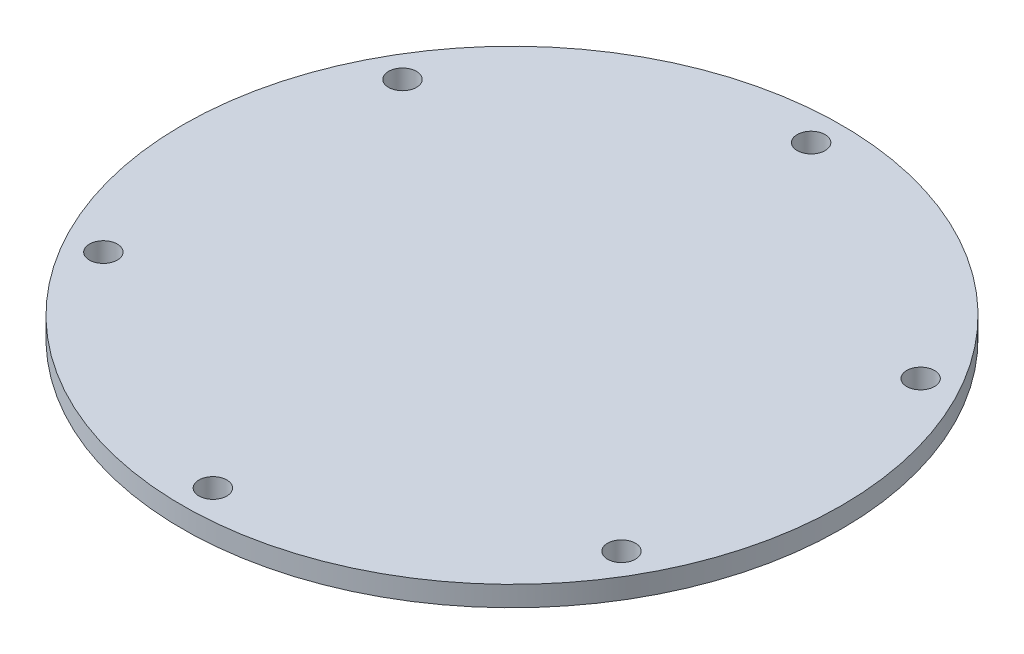
SolidWorks part; units mm, degrees
ref_plane "Alzado" through (0, 0, 0) normal (0, 0, 1) x (1, 0, 0)
ref_plane "Planta" through (0, 0, 0) normal (0, 1, 0) x (1, 0, 0)
ref_plane "Vista lateral" through (0, 0, 0) normal (1, 0, 0) x (0, 0, -1)
sketch "Croquis1" plane through (0, 0, 0) normal (0, 0, 1) x (1, 0, 0)
  line L0 (0, 59.498) -> (0, -59.498) construction
  line L1 (0, 0) -> (-65, 0)
  line L2 (-65, 0) -> (-65, -4)
  line L3 (-65, -4) -> (-44, -4)
  line L4 (-44, -4) -> (-44, -6)
  line L5 (-44, -6) -> (-41, -6)
  line L6 (-41, -6) -> (-41, -4)
  line L7 (-41, -4) -> (0, -4)
  line L8 (0, 0) -> (0, -4)
  point P6 (0, 0)
  dimension "D1" = 65
  dimension "D2" = 4
  dimension "D3" = 6
  dimension "D4" = 44
  dimension "D5" = 3
revolve "Revolución1" add sketch "Croquis1" angle 360 about L0
hole_wizard "Taladro de margen para M51" positions "Croquis4" profile "Croquis5" hole size "M5" standard "DIN"
sketch "Croquis4" plane through (0, -4, 0) normal (0, -1, 0) x (-1, 0, 0)
  circle A0 centre (0, 0) radius 59 construction
  point P5 (0, 59)
  dimension "D1" = 118
sketch "Croquis5" plane through (0, -4, -59) normal (1, 0, 0) x (0, 0, -1)
  line L0 (0, 0) -> (0, 4)
  line L1 (0, 4) -> (2.75, 4)
  line L2 (2.75, 4) -> (2.75, 0)
  line L5 (2.75, 0) -> (0, 0)
  line L11 (0, -6.35) -> (0, 107.95) construction
  dimension "Diámetro de taladro hasta el siguiente" = 5.5
  dimension "Profundidad de taladro hasta el siguiente" = 4
pattern_circular "MatrizC1" count 6 over 360 about axis through (0, 0, 0) along (0, 1, 0) of "Taladro de margen para M51"
equation "\"D1@Croquis1\"=130/2"
equation "\"D4@Croquis1\"=88/2"
